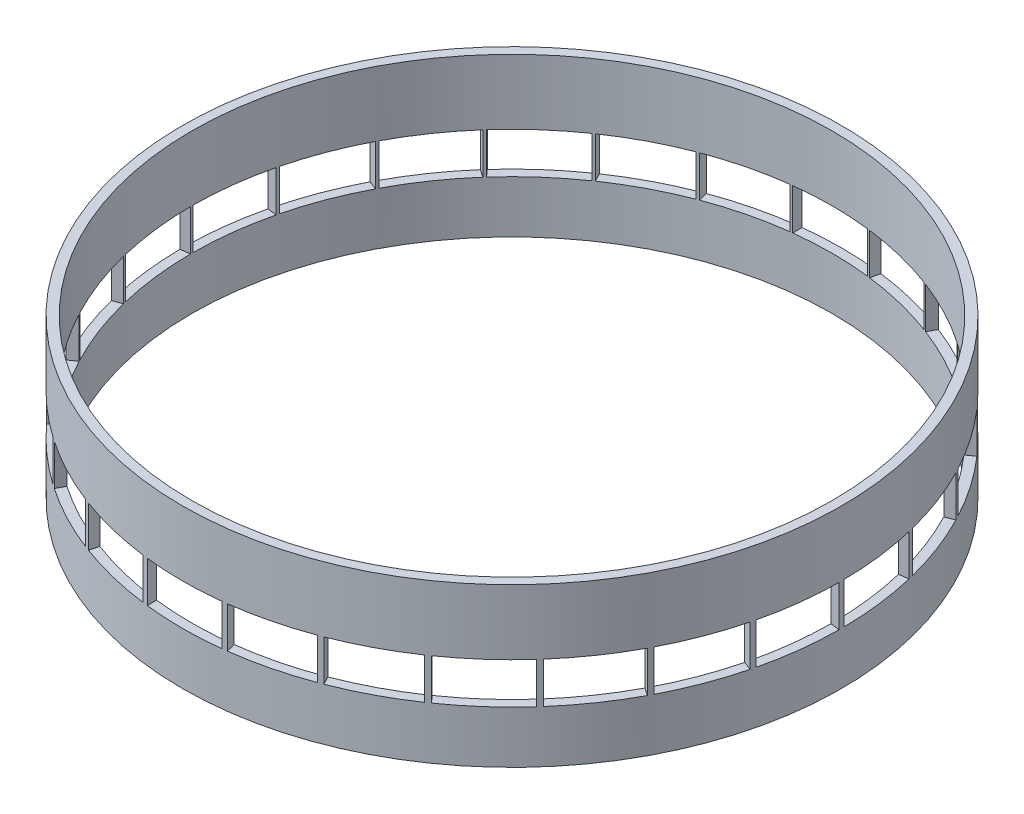
SolidWorks part; units mm, degrees
ref_plane "Front" through (0, 0, 0) normal (0, 0, 1) x (1, 0, 0)
ref_plane "Top" through (0, 0, 0) normal (0, 1, 0) x (1, 0, 0)
ref_plane "Right" through (0, 0, 0) normal (1, 0, 0) x (0, 0, -1)
sketch "Sketch1" plane through (0, 0, 0) normal (0, 1, 0) x (1, 0, 0)
  circle A0 centre (0, 0) radius 85.865
  circle A1 centre (0, 0) radius 88.365
  dimension "D1" = 176.73
  dimension "D2" = 171.73
extrude "Boss-Extrude1" add sketch "Sketch1" along normal blind 42.425
sketch "Sketch2" plane through (0, 0, 0) normal (0, 0, 1) x (1, 0, 0)
  line L1 (-10, 25) -> (10, 25)
  line L2 (-10, 25) -> (-10, 14)
  line L3 (-10, 14) -> (10, 14)
  line L4 (10, 25) -> (10, 14)
  line L5 (-88.365, 0) -> (88.365, 0) construction
  line L6 (-85.865, 0) -> (85.865, 0) construction
  line L7 (0, 0) -> (0, 25) construction
  dimension "D1" = 14
  dimension "D2" = 11
  dimension "D3" = 20
extrude "Cut-Extrude1" cut sketch "Sketch2" against normal through all both and the other way through all
pattern_circular "CirPattern1" count 13 over 360 about axis through (0, 0, 0) along (0, 1, 0) of "Cut-Extrude1"
